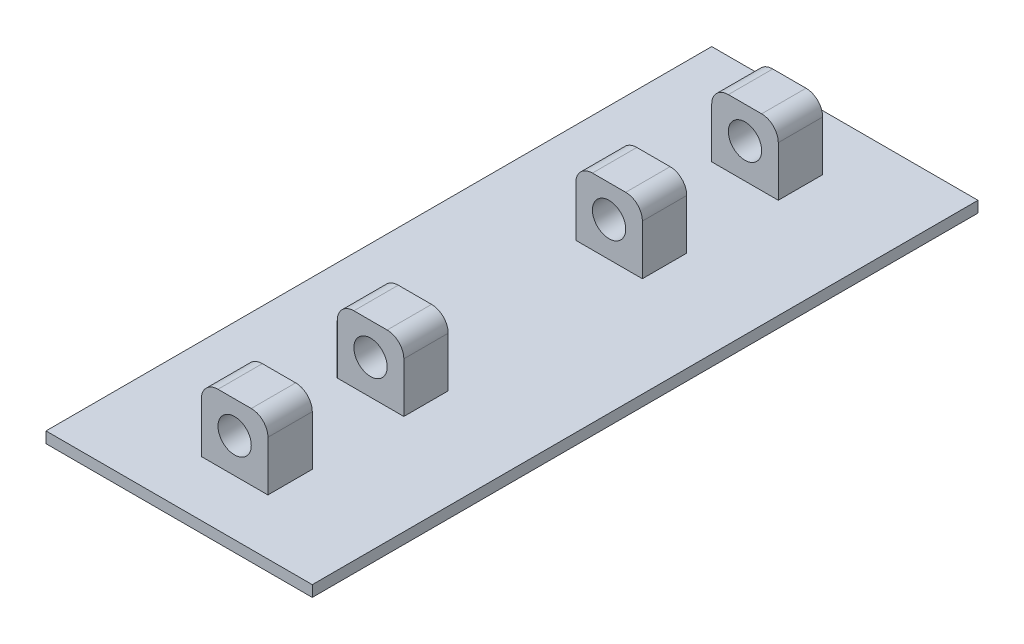
SolidWorks part; units mm, degrees
ref_plane "Front Plane" through (0, 0, 0) normal (0, 0, 1) x (1, 0, 0)
ref_plane "Top Plane" through (0, 0, 0) normal (0, 1, 0) x (1, 0, 0)
ref_plane "Right Plane" through (0, 0, 0) normal (1, 0, 0) x (0, 0, -1)
sketch "Sketch1" plane through (0, 0, 0) normal (0, 1, 0) x (1, 0, 0)
  line L1 (-120, 300) -> (120, 300)
  line L2 (-120, 300) -> (-120, -300)
  line L3 (-120, -300) -> (120, -300)
  line L4 (120, 300) -> (120, -300)
  dimension "D1" = 240
  dimension "D2" = 120
  dimension "D3" = 600
  dimension "D4" = 300
extrude "Extrude1" add sketch "Sketch1" along normal blind 10
ref_plane "Plane1" through (0, 0, 250) normal (0, 0, 1) x (1, 0, 0)
sketch "Sketch2" plane through (0, 0, 250) normal (0, 0, 1) x (1, 0, 0)
  line L1 (-120, 10) -> (120, 10) construction
  line L2 (-30, 10) -> (30, 10)
  line L3 (-30, 10) -> (-30, 55)
  line L4 (-15, 70) -> (15, 70)
  line L5 (30, 10) -> (30, 55)
  line L6 (0, 10) -> (0, 122.3202) construction
  line L7 (0, -67.2761) -> (0, 67.2761) construction
  arc A0 (30, 55) -> (15, 70) centre (15, 55) ccw
  arc A1 (-30, 55) -> (-15, 70) centre (-15, 55) cw
  circle A2 centre (0, 41.2143) radius 15
  point P12 (30, 70)
  dimension "D1" = 30
  dimension "DS_Pin_Hole_Dia" = 30
  dimension "DS_Fillet_Dia" = 15
  dimension "D2" = 60
extrude "Extrude2" add sketch "Sketch2" against normal blind 40
ref_plane "Plane2" through (0, 0, 168.75) normal (0, 0, 1) x (1, 0, 0)
mirror "Mirror1" about plane through (0, 0, 168.75) normal (0, 0, 1) of "Extrude2"
mirror "Mirror2" about plane through (0, 0, 0) normal (0, 0, 1) of "Mirror1", "Extrude2"
